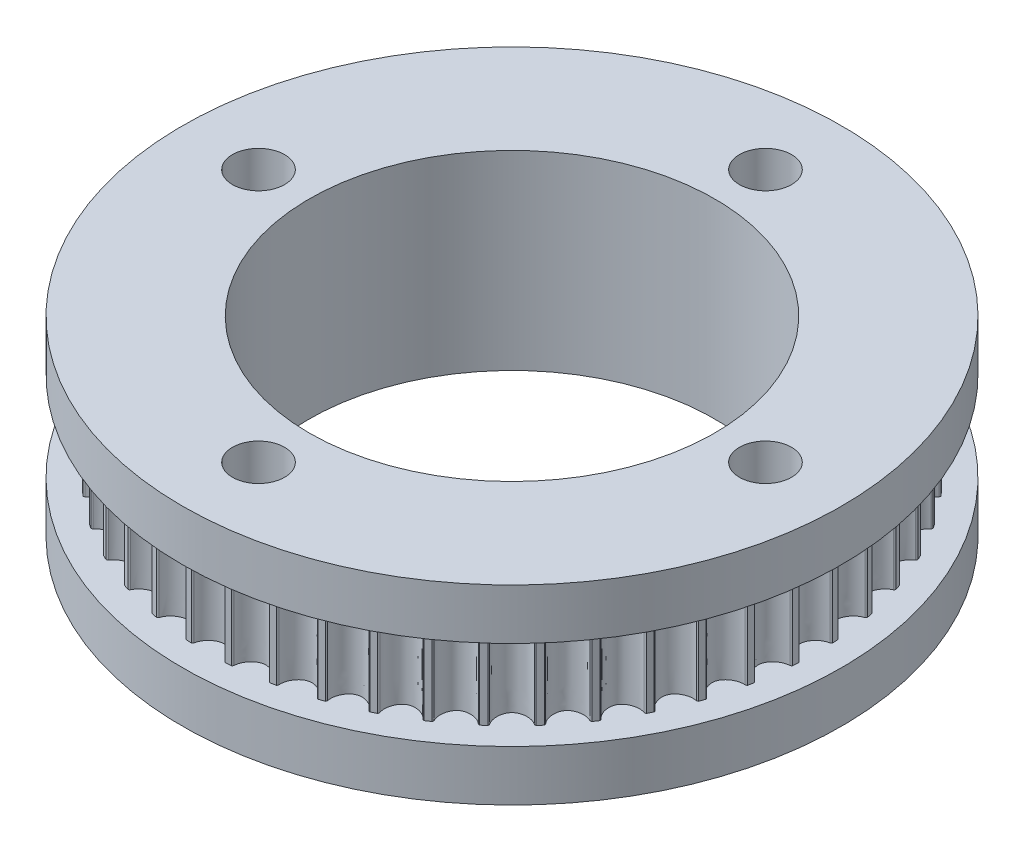
SolidWorks part; units mm, degrees
ref_plane "Front Plane" through (0, 0, 0) normal (0, 0, 1) x (1, 0, 0)
ref_plane "Top Plane" through (0, 0, 0) normal (0, 1, 0) x (1, 0, 0)
ref_plane "Right Plane" through (0, 0, 0) normal (1, 0, 0) x (0, 0, -1)
sketch "Sketch1" plane through (0, 0, 0) normal (0, 1, 0) x (1, 0, 0)
  line L0 (-1.9939, 38.0478) -> (1.9939, 38.0478) construction
  line L1 (0, 38.0478) -> (0, 36.0666) construction
  line L2 (-1.1557, 36.5238) -> (1.1557, 36.5238) construction
  circle A1 centre (0, 0) radius 38.1
  arc A2 (-1.9773, 37.8753) -> (-2.1224, 38.0408) centre (-2.3241, 37.7176) ccw
  arc A3 (1.9773, 37.8753) -> (2.1224, 38.0408) centre (2.3241, 37.7176) cw
  arc A4 (2.9834, 37.8094) -> (2.8611, 37.9924) centre (2.6189, 37.6983) ccw
  arc A5 (6.9041, 37.2932) -> (7.0696, 37.4384) centre (7.2274, 37.0916) cw
  arc A6 (7.8929, 37.0965) -> (7.7956, 37.294) centre (7.5171, 37.0339) ccw
  arc A7 (11.7127, 36.073) -> (11.8958, 36.1953) centre (12.0069, 35.8309) cw
  arc A8 (12.6675, 35.7489) -> (12.5967, 35.9574) centre (12.2867, 35.7359) ccw
  arc A9 (16.321, 34.2355) -> (16.5185, 34.3329) centre (16.5811, 33.9571) cw
  arc A10 (17.2253, 33.7896) -> (17.1823, 34.0055) centre (16.8461, 33.8264) ccw
  arc A11 (20.65, 31.8123) -> (20.8585, 31.8831) centre (20.8715, 31.5023) cw
  arc A12 (21.4883, 31.2522) -> (21.474, 31.4719) centre (21.1172, 31.3382) ccw
  arc A13 (24.6257, 28.8448) -> (24.8416, 28.8878) centre (24.8048, 28.5086) cw
  arc A14 (25.3837, 28.18) -> (25.3982, 28.3997) centre (25.027, 28.3138) ccw
  arc A15 (28.18, 25.3837) -> (28.3997, 25.3982) centre (28.3138, 25.027) cw
  arc A16 (28.8448, 24.6257) -> (28.8878, 24.8416) centre (28.5086, 24.8048) ccw
  arc A17 (31.2522, 21.4883) -> (31.4719, 21.474) centre (31.3382, 21.1172) cw
  arc A18 (31.8123, 20.65) -> (31.8831, 20.8585) centre (31.5023, 20.8715) ccw
  arc A19 (33.7896, 17.2253) -> (34.0055, 17.1823) centre (33.8264, 16.8461) cw
  arc A20 (34.2355, 16.321) -> (34.3329, 16.5185) centre (33.9571, 16.5811) ccw
  arc A21 (35.7489, 12.6675) -> (35.9574, 12.5967) centre (35.7359, 12.2867) cw
  arc A22 (36.073, 11.7127) -> (36.1953, 11.8958) centre (35.8309, 12.0069) ccw
  arc A23 (37.0965, 7.8929) -> (37.294, 7.7956) centre (37.0339, 7.5171) cw
  arc A24 (37.2932, 6.9041) -> (37.4384, 7.0696) centre (37.0916, 7.2274) ccw
  arc A25 (37.8094, 2.9834) -> (37.9924, 2.8611) centre (37.6983, 2.6189) cw
  arc A26 (37.8753, 1.9773) -> (38.0408, 2.1224) centre (37.7176, 2.3241) ccw
  arc A27 (37.8753, -1.9773) -> (38.0408, -2.1224) centre (37.7176, -2.3241) cw
  arc A28 (37.8094, -2.9834) -> (37.9924, -2.8611) centre (37.6983, -2.6189) ccw
  arc A29 (37.2932, -6.9041) -> (37.4384, -7.0696) centre (37.0916, -7.2274) cw
  arc A30 (37.0965, -7.8929) -> (37.294, -7.7956) centre (37.0339, -7.5171) ccw
  arc A31 (36.073, -11.7127) -> (36.1953, -11.8958) centre (35.8309, -12.0069) cw
  arc A32 (35.7489, -12.6675) -> (35.9574, -12.5967) centre (35.7359, -12.2867) ccw
  arc A33 (34.2355, -16.321) -> (34.3329, -16.5185) centre (33.9571, -16.5811) cw
  arc A34 (33.7896, -17.2253) -> (34.0055, -17.1823) centre (33.8264, -16.8461) ccw
  arc A35 (31.8123, -20.65) -> (31.8831, -20.8585) centre (31.5023, -20.8715) cw
  arc A36 (31.2522, -21.4883) -> (31.4719, -21.474) centre (31.3382, -21.1172) ccw
  arc A37 (28.8448, -24.6257) -> (28.8878, -24.8416) centre (28.5086, -24.8048) cw
  arc A38 (28.18, -25.3837) -> (28.3997, -25.3982) centre (28.3138, -25.027) ccw
  arc A39 (25.3837, -28.18) -> (25.3982, -28.3997) centre (25.027, -28.3138) cw
  arc A40 (24.6257, -28.8448) -> (24.8416, -28.8878) centre (24.8048, -28.5086) ccw
  arc A41 (21.4883, -31.2522) -> (21.474, -31.4719) centre (21.1172, -31.3382) cw
  arc A42 (20.65, -31.8123) -> (20.8585, -31.8831) centre (20.8715, -31.5023) ccw
  arc A43 (17.2253, -33.7896) -> (17.1823, -34.0055) centre (16.8461, -33.8264) cw
  arc A44 (16.321, -34.2355) -> (16.5185, -34.3329) centre (16.5811, -33.9571) ccw
  arc A45 (12.6675, -35.7489) -> (12.5967, -35.9574) centre (12.2867, -35.7359) cw
  arc A46 (11.7127, -36.073) -> (11.8958, -36.1953) centre (12.0069, -35.8309) ccw
  arc A47 (7.8929, -37.0965) -> (7.7956, -37.294) centre (7.5171, -37.0339) cw
  arc A48 (6.9041, -37.2932) -> (7.0696, -37.4384) centre (7.2274, -37.0916) ccw
  arc A49 (2.9834, -37.8094) -> (2.8611, -37.9924) centre (2.6189, -37.6983) cw
  arc A50 (1.9773, -37.8753) -> (2.1224, -38.0408) centre (2.3241, -37.7176) ccw
  arc A51 (-1.9773, -37.8753) -> (-2.1224, -38.0408) centre (-2.3241, -37.7176) cw
  arc A52 (-2.9834, -37.8094) -> (-2.8611, -37.9924) centre (-2.6189, -37.6983) ccw
  arc A53 (-6.9041, -37.2932) -> (-7.0696, -37.4384) centre (-7.2274, -37.0916) cw
  arc A54 (-7.8929, -37.0965) -> (-7.7956, -37.294) centre (-7.5171, -37.0339) ccw
  arc A55 (-11.7127, -36.073) -> (-11.8958, -36.1953) centre (-12.0069, -35.8309) cw
  arc A56 (-12.6675, -35.7489) -> (-12.5967, -35.9574) centre (-12.2867, -35.7359) ccw
  arc A57 (-16.321, -34.2355) -> (-16.5185, -34.3329) centre (-16.5811, -33.9571) cw
  arc A58 (-17.2253, -33.7896) -> (-17.1823, -34.0055) centre (-16.8461, -33.8264) ccw
  arc A59 (-20.65, -31.8123) -> (-20.8585, -31.8831) centre (-20.8715, -31.5023) cw
  arc A60 (-21.4883, -31.2522) -> (-21.474, -31.4719) centre (-21.1172, -31.3382) ccw
  arc A61 (-24.6257, -28.8448) -> (-24.8416, -28.8878) centre (-24.8048, -28.5086) cw
  arc A62 (-25.3837, -28.18) -> (-25.3982, -28.3997) centre (-25.027, -28.3138) ccw
  arc A63 (-28.18, -25.3837) -> (-28.3997, -25.3982) centre (-28.3138, -25.027) cw
  arc A64 (-28.8448, -24.6257) -> (-28.8878, -24.8416) centre (-28.5086, -24.8048) ccw
  arc A65 (-31.2522, -21.4883) -> (-31.4719, -21.474) centre (-31.3382, -21.1172) cw
  arc A66 (-31.8123, -20.65) -> (-31.8831, -20.8585) centre (-31.5023, -20.8715) ccw
  arc A67 (-33.7896, -17.2253) -> (-34.0055, -17.1823) centre (-33.8264, -16.8461) cw
  arc A68 (-34.2355, -16.321) -> (-34.3329, -16.5185) centre (-33.9571, -16.5811) ccw
  arc A69 (-35.7489, -12.6675) -> (-35.9574, -12.5967) centre (-35.7359, -12.2867) cw
  arc A70 (-36.073, -11.7127) -> (-36.1953, -11.8958) centre (-35.8309, -12.0069) ccw
  arc A71 (-37.0965, -7.8929) -> (-37.294, -7.7956) centre (-37.0339, -7.5171) cw
  arc A72 (-37.2932, -6.9041) -> (-37.4384, -7.0696) centre (-37.0916, -7.2274) ccw
  arc A73 (-37.8094, -2.9834) -> (-37.9924, -2.8611) centre (-37.6983, -2.6189) cw
  arc A74 (-37.8753, -1.9773) -> (-38.0408, -2.1224) centre (-37.7176, -2.3241) ccw
  arc A75 (-37.8753, 1.9773) -> (-38.0408, 2.1224) centre (-37.7176, 2.3241) cw
  arc A76 (-37.8094, 2.9834) -> (-37.9924, 2.8611) centre (-37.6983, 2.6189) ccw
  arc A77 (-37.2932, 6.9041) -> (-37.4384, 7.0696) centre (-37.0916, 7.2274) cw
  arc A78 (-37.0965, 7.8929) -> (-37.294, 7.7956) centre (-37.0339, 7.5171) ccw
  arc A79 (-36.073, 11.7127) -> (-36.1953, 11.8958) centre (-35.8309, 12.0069) cw
  arc A80 (-35.7489, 12.6675) -> (-35.9574, 12.5967) centre (-35.7359, 12.2867) ccw
  arc A81 (-34.2355, 16.321) -> (-34.3329, 16.5185) centre (-33.9571, 16.5811) cw
  arc A82 (-33.7896, 17.2253) -> (-34.0055, 17.1823) centre (-33.8264, 16.8461) ccw
  arc A83 (-31.8123, 20.65) -> (-31.8831, 20.8585) centre (-31.5023, 20.8715) cw
  arc A84 (-31.2522, 21.4883) -> (-31.4719, 21.474) centre (-31.3382, 21.1172) ccw
  arc A85 (-28.8448, 24.6257) -> (-28.8878, 24.8416) centre (-28.5086, 24.8048) cw
  arc A86 (-28.18, 25.3837) -> (-28.3997, 25.3982) centre (-28.3138, 25.027) ccw
  arc A87 (-25.3837, 28.18) -> (-25.3982, 28.3997) centre (-25.027, 28.3138) cw
  arc A88 (-24.6257, 28.8448) -> (-24.8416, 28.8878) centre (-24.8048, 28.5086) ccw
  arc A89 (-21.4883, 31.2522) -> (-21.474, 31.4719) centre (-21.1172, 31.3382) cw
  arc A90 (-20.65, 31.8123) -> (-20.8585, 31.8831) centre (-20.8715, 31.5023) ccw
  arc A91 (-17.2253, 33.7896) -> (-17.1823, 34.0055) centre (-16.8461, 33.8264) cw
  arc A92 (-16.321, 34.2355) -> (-16.5185, 34.3329) centre (-16.5811, 33.9571) ccw
  arc A93 (-12.6675, 35.7489) -> (-12.5967, 35.9574) centre (-12.2867, 35.7359) cw
  arc A94 (-11.7127, 36.073) -> (-11.8958, 36.1953) centre (-12.0069, 35.8309) ccw
  arc A95 (-7.8929, 37.0965) -> (-7.7956, 37.294) centre (-7.5171, 37.0339) cw
  arc A96 (-6.9041, 37.2932) -> (-7.0696, 37.4384) centre (-7.2274, 37.0916) ccw
  arc A97 (-2.9834, 37.8094) -> (-2.8611, 37.9924) centre (-2.6189, 37.6983) cw
  spline S0 degree 3 poles (-1.9773, 37.8753) (-1.9007, 37.3761) (-1.3278, 36.4709) (0, 35.8873) (1.3278, 36.4709) (1.9007, 37.3761) (1.9773, 37.8753) knots 0.030185 0.030185 0.030185 0.030185 0.291618 0.5 0.708382 0.969815 0.969815 0.969815 0.969815
  spline S1 degree 3 poles (2.9834, 37.8094) (2.9941, 37.3044) (3.4439, 36.3322) (4.6842, 35.5802) (6.0769, 35.9856) (6.763, 36.8082) (6.9041, 37.2932) knots 0.030185 0.030185 0.030185 0.030185 0.291618 0.5 0.708382 0.969815 0.969815 0.969815 0.969815
  spline S2 degree 3 poles (7.8929, 37.0965) (7.8377, 36.5945) (8.1568, 35.5719) (9.2883, 34.6644) (10.7219, 34.8845) (11.5096, 35.6106) (11.7127, 36.073) knots 0.030185 0.030185 0.030185 0.030185 0.291618 0.5 0.708382 0.969815 0.969815 0.969815 0.969815
  spline S3 degree 3 poles (12.6675, 35.7489) (12.5472, 35.2584) (12.7301, 34.2029) (13.7335, 33.1555) (15.1836, 33.1866) (16.0592, 33.8036) (16.321, 34.2355) knots 0.030185 0.030185 0.030185 0.030185 0.291618 0.5 0.708382 0.969815 0.969815 0.969815 0.969815
  spline S4 degree 3 poles (17.2253, 33.7896) (17.042, 33.319) (17.0855, 32.2487) (17.9436, 31.0793) (19.3854, 30.9208) (20.3341, 31.4183) (20.65, 31.8123) knots 0.030185 0.030185 0.030185 0.030185 0.291618 0.5 0.708382 0.969815 0.969815 0.969815 0.969815
  spline S5 degree 3 poles (21.4883, 31.2522) (21.2452, 30.8095) (21.1487, 29.7427) (21.8468, 28.4713) (23.2555, 28.126) (24.2611, 28.4954) (24.6257, 28.8448) knots 0.030185 0.030185 0.030185 0.030185 0.291618 0.5 0.708382 0.969815 0.969815 0.969815 0.969815
  spline S6 degree 3 poles (25.3837, 28.18) (25.0849, 27.7729) (24.8499, 26.7277) (25.3761, 25.3761) (26.7277, 24.8499) (27.7729, 25.0849) (28.18, 25.3837) knots 0.030185 0.030185 0.030185 0.030185 0.291618 0.5 0.708382 0.969815 0.969815 0.969815 0.969815
  spline S7 degree 3 poles (28.8448, 24.6257) (28.4954, 24.2611) (28.126, 23.2555) (28.4713, 21.8468) (29.7427, 21.1487) (30.8095, 21.2452) (31.2522, 21.4883) knots 0.030185 0.030185 0.030185 0.030185 0.291618 0.5 0.708382 0.969815 0.969815 0.969815 0.969815
  spline S8 degree 3 poles (31.8123, 20.65) (31.4183, 20.3341) (30.9208, 19.3854) (31.0793, 17.9436) (32.2487, 17.0855) (33.319, 17.042) (33.7896, 17.2253) knots 0.030185 0.030185 0.030185 0.030185 0.291618 0.5 0.708382 0.969815 0.969815 0.969815 0.969815
  spline S9 degree 3 poles (34.2355, 16.321) (33.8036, 16.0592) (33.1866, 15.1836) (33.1555, 13.7335) (34.2029, 12.7301) (35.2584, 12.5472) (35.7489, 12.6675) knots 0.030185 0.030185 0.030185 0.030185 0.291618 0.5 0.708382 0.969815 0.969815 0.969815 0.969815
  spline S10 degree 3 poles (36.073, 11.7127) (35.6106, 11.5096) (34.8845, 10.7219) (34.6644, 9.2883) (35.5719, 8.1568) (36.5945, 7.8377) (37.0965, 7.8929) knots 0.030185 0.030185 0.030185 0.030185 0.291618 0.5 0.708382 0.969815 0.969815 0.969815 0.969815
  spline S11 degree 3 poles (37.2932, 6.9041) (36.8082, 6.763) (35.9856, 6.0769) (35.5802, 4.6842) (36.3322, 3.4439) (37.3044, 2.9941) (37.8094, 2.9834) knots 0.030185 0.030185 0.030185 0.030185 0.291618 0.5 0.708382 0.969815 0.969815 0.969815 0.969815
  spline S12 degree 3 poles (37.8753, 1.9773) (37.3761, 1.9007) (36.4709, 1.3278) (35.8873, 0) (36.4709, -1.3278) (37.3761, -1.9007) (37.8753, -1.9773) knots 0.030185 0.030185 0.030185 0.030185 0.291618 0.5 0.708382 0.969815 0.969815 0.969815 0.969815
  spline S13 degree 3 poles (37.8094, -2.9834) (37.3044, -2.9941) (36.3322, -3.4439) (35.5802, -4.6842) (35.9856, -6.0769) (36.8082, -6.763) (37.2932, -6.9041) knots 0.030185 0.030185 0.030185 0.030185 0.291618 0.5 0.708382 0.969815 0.969815 0.969815 0.969815
  spline S14 degree 3 poles (37.0965, -7.8929) (36.5945, -7.8377) (35.5719, -8.1568) (34.6644, -9.2883) (34.8845, -10.7219) (35.6106, -11.5096) (36.073, -11.7127) knots 0.030185 0.030185 0.030185 0.030185 0.291618 0.5 0.708382 0.969815 0.969815 0.969815 0.969815
  spline S15 degree 3 poles (35.7489, -12.6675) (35.2584, -12.5472) (34.2029, -12.7301) (33.1555, -13.7335) (33.1866, -15.1836) (33.8036, -16.0592) (34.2355, -16.321) knots 0.030185 0.030185 0.030185 0.030185 0.291618 0.5 0.708382 0.969815 0.969815 0.969815 0.969815
  spline S16 degree 3 poles (33.7896, -17.2253) (33.319, -17.042) (32.2487, -17.0855) (31.0793, -17.9436) (30.9208, -19.3854) (31.4183, -20.3341) (31.8123, -20.65) knots 0.030185 0.030185 0.030185 0.030185 0.291618 0.5 0.708382 0.969815 0.969815 0.969815 0.969815
  spline S17 degree 3 poles (31.2522, -21.4883) (30.8095, -21.2452) (29.7427, -21.1487) (28.4713, -21.8468) (28.126, -23.2555) (28.4954, -24.2611) (28.8448, -24.6257) knots 0.030185 0.030185 0.030185 0.030185 0.291618 0.5 0.708382 0.969815 0.969815 0.969815 0.969815
  spline S18 degree 3 poles (28.18, -25.3837) (27.7729, -25.0849) (26.7277, -24.8499) (25.3761, -25.3761) (24.8499, -26.7277) (25.0849, -27.7729) (25.3837, -28.18) knots 0.030185 0.030185 0.030185 0.030185 0.291618 0.5 0.708382 0.969815 0.969815 0.969815 0.969815
  spline S19 degree 3 poles (24.6257, -28.8448) (24.2611, -28.4954) (23.2555, -28.126) (21.8468, -28.4713) (21.1487, -29.7427) (21.2452, -30.8095) (21.4883, -31.2522) knots 0.030185 0.030185 0.030185 0.030185 0.291618 0.5 0.708382 0.969815 0.969815 0.969815 0.969815
  spline S20 degree 3 poles (20.65, -31.8123) (20.3341, -31.4183) (19.3854, -30.9208) (17.9436, -31.0793) (17.0855, -32.2487) (17.042, -33.319) (17.2253, -33.7896) knots 0.030185 0.030185 0.030185 0.030185 0.291618 0.5 0.708382 0.969815 0.969815 0.969815 0.969815
  spline S21 degree 3 poles (16.321, -34.2355) (16.0592, -33.8036) (15.1836, -33.1866) (13.7335, -33.1555) (12.7301, -34.2029) (12.5472, -35.2584) (12.6675, -35.7489) knots 0.030185 0.030185 0.030185 0.030185 0.291618 0.5 0.708382 0.969815 0.969815 0.969815 0.969815
  spline S22 degree 3 poles (11.7127, -36.073) (11.5096, -35.6106) (10.7219, -34.8845) (9.2883, -34.6644) (8.1568, -35.5719) (7.8377, -36.5945) (7.8929, -37.0965) knots 0.030185 0.030185 0.030185 0.030185 0.291618 0.5 0.708382 0.969815 0.969815 0.969815 0.969815
  spline S23 degree 3 poles (6.9041, -37.2932) (6.763, -36.8082) (6.0769, -35.9856) (4.6842, -35.5802) (3.4439, -36.3322) (2.9941, -37.3044) (2.9834, -37.8094) knots 0.030185 0.030185 0.030185 0.030185 0.291618 0.5 0.708382 0.969815 0.969815 0.969815 0.969815
  spline S24 degree 3 poles (1.9773, -37.8753) (1.9007, -37.3761) (1.3278, -36.4709) (0, -35.8873) (-1.3278, -36.4709) (-1.9007, -37.3761) (-1.9773, -37.8753) knots 0.030185 0.030185 0.030185 0.030185 0.291618 0.5 0.708382 0.969815 0.969815 0.969815 0.969815
  spline S25 degree 3 poles (-2.9834, -37.8094) (-2.9941, -37.3044) (-3.4439, -36.3322) (-4.6842, -35.5802) (-6.0769, -35.9856) (-6.763, -36.8082) (-6.9041, -37.2932) knots 0.030185 0.030185 0.030185 0.030185 0.291618 0.5 0.708382 0.969815 0.969815 0.969815 0.969815
  spline S26 degree 3 poles (-7.8929, -37.0965) (-7.8377, -36.5945) (-8.1568, -35.5719) (-9.2883, -34.6644) (-10.7219, -34.8845) (-11.5096, -35.6106) (-11.7127, -36.073) knots 0.030185 0.030185 0.030185 0.030185 0.291618 0.5 0.708382 0.969815 0.969815 0.969815 0.969815
  spline S27 degree 3 poles (-12.6675, -35.7489) (-12.5472, -35.2584) (-12.7301, -34.2029) (-13.7335, -33.1555) (-15.1836, -33.1866) (-16.0592, -33.8036) (-16.321, -34.2355) knots 0.030185 0.030185 0.030185 0.030185 0.291618 0.5 0.708382 0.969815 0.969815 0.969815 0.969815
  spline S28 degree 3 poles (-17.2253, -33.7896) (-17.042, -33.319) (-17.0855, -32.2487) (-17.9436, -31.0793) (-19.3854, -30.9208) (-20.3341, -31.4183) (-20.65, -31.8123) knots 0.030185 0.030185 0.030185 0.030185 0.291618 0.5 0.708382 0.969815 0.969815 0.969815 0.969815
  spline S29 degree 3 poles (-21.4883, -31.2522) (-21.2452, -30.8095) (-21.1487, -29.7427) (-21.8468, -28.4713) (-23.2555, -28.126) (-24.2611, -28.4954) (-24.6257, -28.8448) knots 0.030185 0.030185 0.030185 0.030185 0.291618 0.5 0.708382 0.969815 0.969815 0.969815 0.969815
  spline S30 degree 3 poles (-25.3837, -28.18) (-25.0849, -27.7729) (-24.8499, -26.7277) (-25.3761, -25.3761) (-26.7277, -24.8499) (-27.7729, -25.0849) (-28.18, -25.3837) knots 0.030185 0.030185 0.030185 0.030185 0.291618 0.5 0.708382 0.969815 0.969815 0.969815 0.969815
  spline S31 degree 3 poles (-28.8448, -24.6257) (-28.4954, -24.2611) (-28.126, -23.2555) (-28.4713, -21.8468) (-29.7427, -21.1487) (-30.8095, -21.2452) (-31.2522, -21.4883) knots 0.030185 0.030185 0.030185 0.030185 0.291618 0.5 0.708382 0.969815 0.969815 0.969815 0.969815
  spline S32 degree 3 poles (-31.8123, -20.65) (-31.4183, -20.3341) (-30.9208, -19.3854) (-31.0793, -17.9436) (-32.2487, -17.0855) (-33.319, -17.042) (-33.7896, -17.2253) knots 0.030185 0.030185 0.030185 0.030185 0.291618 0.5 0.708382 0.969815 0.969815 0.969815 0.969815
  spline S33 degree 3 poles (-34.2355, -16.321) (-33.8036, -16.0592) (-33.1866, -15.1836) (-33.1555, -13.7335) (-34.2029, -12.7301) (-35.2584, -12.5472) (-35.7489, -12.6675) knots 0.030185 0.030185 0.030185 0.030185 0.291618 0.5 0.708382 0.969815 0.969815 0.969815 0.969815
  spline S34 degree 3 poles (-36.073, -11.7127) (-35.6106, -11.5096) (-34.8845, -10.7219) (-34.6644, -9.2883) (-35.5719, -8.1568) (-36.5945, -7.8377) (-37.0965, -7.8929) knots 0.030185 0.030185 0.030185 0.030185 0.291618 0.5 0.708382 0.969815 0.969815 0.969815 0.969815
  spline S35 degree 3 poles (-37.2932, -6.9041) (-36.8082, -6.763) (-35.9856, -6.0769) (-35.5802, -4.6842) (-36.3322, -3.4439) (-37.3044, -2.9941) (-37.8094, -2.9834) knots 0.030185 0.030185 0.030185 0.030185 0.291618 0.5 0.708382 0.969815 0.969815 0.969815 0.969815
  spline S36 degree 3 poles (-37.8753, -1.9773) (-37.3761, -1.9007) (-36.4709, -1.3278) (-35.8873, 0) (-36.4709, 1.3278) (-37.3761, 1.9007) (-37.8753, 1.9773) knots 0.030185 0.030185 0.030185 0.030185 0.291618 0.5 0.708382 0.969815 0.969815 0.969815 0.969815
  spline S37 degree 3 poles (-37.8094, 2.9834) (-37.3044, 2.9941) (-36.3322, 3.4439) (-35.5802, 4.6842) (-35.9856, 6.0769) (-36.8082, 6.763) (-37.2932, 6.9041) knots 0.030185 0.030185 0.030185 0.030185 0.291618 0.5 0.708382 0.969815 0.969815 0.969815 0.969815
  spline S38 degree 3 poles (-37.0965, 7.8929) (-36.5945, 7.8377) (-35.5719, 8.1568) (-34.6644, 9.2883) (-34.8845, 10.7219) (-35.6106, 11.5096) (-36.073, 11.7127) knots 0.030185 0.030185 0.030185 0.030185 0.291618 0.5 0.708382 0.969815 0.969815 0.969815 0.969815
  spline S39 degree 3 poles (-35.7489, 12.6675) (-35.2584, 12.5472) (-34.2029, 12.7301) (-33.1555, 13.7335) (-33.1866, 15.1836) (-33.8036, 16.0592) (-34.2355, 16.321) knots 0.030185 0.030185 0.030185 0.030185 0.291618 0.5 0.708382 0.969815 0.969815 0.969815 0.969815
  spline S40 degree 3 poles (-33.7896, 17.2253) (-33.319, 17.042) (-32.2487, 17.0855) (-31.0793, 17.9436) (-30.9208, 19.3854) (-31.4183, 20.3341) (-31.8123, 20.65) knots 0.030185 0.030185 0.030185 0.030185 0.291618 0.5 0.708382 0.969815 0.969815 0.969815 0.969815
  spline S41 degree 3 poles (-31.2522, 21.4883) (-30.8095, 21.2452) (-29.7427, 21.1487) (-28.4713, 21.8468) (-28.126, 23.2555) (-28.4954, 24.2611) (-28.8448, 24.6257) knots 0.030185 0.030185 0.030185 0.030185 0.291618 0.5 0.708382 0.969815 0.969815 0.969815 0.969815
  spline S42 degree 3 poles (-28.18, 25.3837) (-27.7729, 25.0849) (-26.7277, 24.8499) (-25.3761, 25.3761) (-24.8499, 26.7277) (-25.0849, 27.7729) (-25.3837, 28.18) knots 0.030185 0.030185 0.030185 0.030185 0.291618 0.5 0.708382 0.969815 0.969815 0.969815 0.969815
  spline S43 degree 3 poles (-24.6257, 28.8448) (-24.2611, 28.4954) (-23.2555, 28.126) (-21.8468, 28.4713) (-21.1487, 29.7427) (-21.2452, 30.8095) (-21.4883, 31.2522) knots 0.030185 0.030185 0.030185 0.030185 0.291618 0.5 0.708382 0.969815 0.969815 0.969815 0.969815
  spline S44 degree 3 poles (-20.65, 31.8123) (-20.3341, 31.4183) (-19.3854, 30.9208) (-17.9436, 31.0793) (-17.0855, 32.2487) (-17.042, 33.319) (-17.2253, 33.7896) knots 0.030185 0.030185 0.030185 0.030185 0.291618 0.5 0.708382 0.969815 0.969815 0.969815 0.969815
  spline S45 degree 3 poles (-16.321, 34.2355) (-16.0592, 33.8036) (-15.1836, 33.1866) (-13.7335, 33.1555) (-12.7301, 34.2029) (-12.5472, 35.2584) (-12.6675, 35.7489) knots 0.030185 0.030185 0.030185 0.030185 0.291618 0.5 0.708382 0.969815 0.969815 0.969815 0.969815
  spline S46 degree 3 poles (-11.7127, 36.073) (-11.5096, 35.6106) (-10.7219, 34.8845) (-9.2883, 34.6644) (-8.1568, 35.5719) (-7.8377, 36.5945) (-7.8929, 37.0965) knots 0.030185 0.030185 0.030185 0.030185 0.291618 0.5 0.708382 0.969815 0.969815 0.969815 0.969815
  spline S47 degree 3 poles (-6.9041, 37.2932) (-6.763, 36.8082) (-6.0769, 35.9856) (-4.6842, 35.5802) (-3.4439, 36.3322) (-2.9941, 37.3044) (-2.9834, 37.8094) knots 0.030185 0.030185 0.030185 0.030185 0.291618 0.5 0.708382 0.969815 0.969815 0.969815 0.969815
  point P8 (-2.3241, 37.7176)
  point P14 (0, 36.5238)
  point P447 (0, 0)
  dimension "D2" = 76.2
  dimension "D9" = 0.762
  dimension "D10" = 5.7657
  dimension "D3" = 3.9878
  dimension "D4" = 1.9812
  dimension "D5" = 2.3114
  dimension "D6" = 0.4572
  dimension "D7" = 0.3302
  dimension "D8" = 0.3302
  dimension "D11" = 48
extrude "Boss-Extrude1" add sketch "Sketch1" along normal blind 11.176 contours S47 A96 A1 A95 S46 A94 A93 S45 A92 A91 S44 A90 A89 S43 A88 A87 S42 A86 A85 S41 A84 A83 S40 A82 A81 S39 A80 A79 S38 A78 A77 S37 A76 A75 S36 A74 A73 S35 A72
sketch "Sketch2" plane through (0, 11.176, 0) normal (0, 1, 0) x (1, 0, 0)
  circle A0 centre (0, 0) radius 41.275
  dimension "D1" = 82.55
extrude "Boss-Extrude2" add sketch "Sketch2" along normal blind 6.35
sketch "Sketch4" plane through (0, 0, 0) normal (0, -1, 0) x (1, 0, 0)
  circle A0 centre (0, 0) radius 41.275
  dimension "D1" = 82.55
extrude "Boss-Extrude3" add sketch "Sketch4" along normal blind 6.35
sketch "Sketch5" plane through (0, 17.526, 0) normal (0, 1, 0) x (1, 0, 0)
  circle A0 centre (0, 0) radius 25.4
  circle A1 centre (0, 31.75) radius 3.2639
  circle A2 centre (31.75, 0) radius 3.2639
  circle A3 centre (0, -31.75) radius 3.2639
  circle A4 centre (-31.75, 0) radius 3.2639
  point P14 (0, 0)
  dimension "D1" = 50.8
  dimension "D2" = 6.5278
  dimension "D4" = 4
  dimension "D3" = 31.75
extrude "Cut-Extrude1" cut sketch "Sketch5" against normal through all
